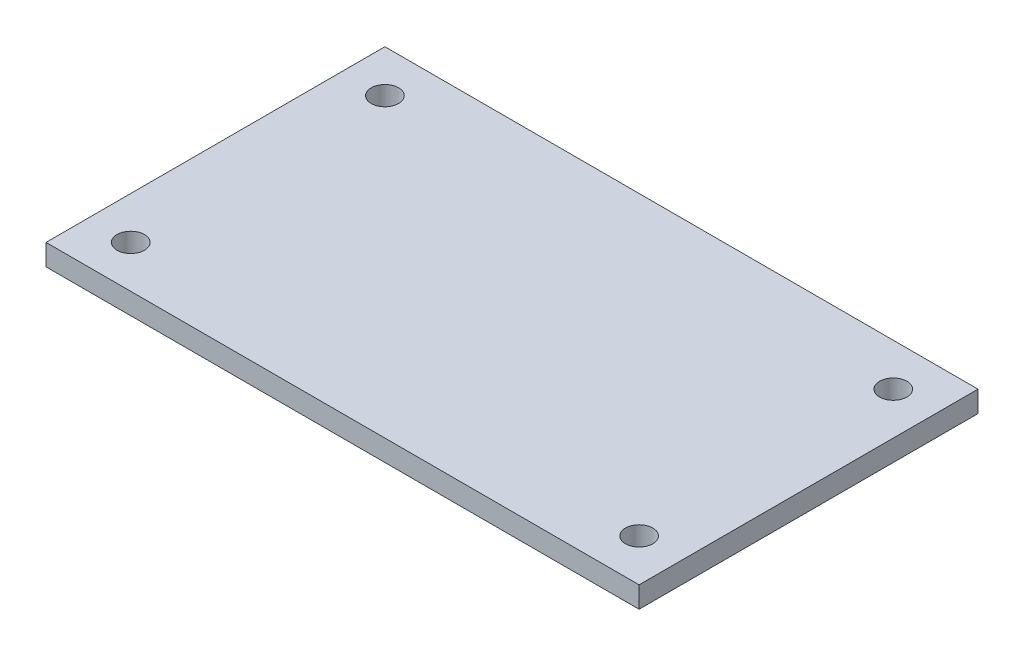
SolidWorks part; units mm, degrees
ref_plane "Front Plane" through (0, 0, 0) normal (0, 0, 1) x (1, 0, 0)
ref_plane "Top Plane" through (0, 0, 0) normal (0, 1, 0) x (1, 0, 0)
ref_plane "Right Plane" through (0, 0, 0) normal (1, 0, 0) x (0, 0, -1)
sketch "Sketch1" plane through (0, 0, 0) normal (0, 1, 0) x (1, 0, 0)
  line L0 (0, 50.8) -> (0, -50.8) construction
  line L1 (-88.9, -50.8) -> (88.9, -50.8)
  line L2 (-88.9, -50.8) -> (-88.9, 50.8)
  line L3 (-88.9, 50.8) -> (88.9, 50.8)
  line L4 (88.9, -50.8) -> (88.9, 50.8)
  line L5 (-88.9, -50.8) -> (88.9, 50.8) construction
  line L6 (-88.9, 50.8) -> (88.9, -50.8) construction
  line L7 (-88.9, 0) -> (88.9, 0) construction
  line L8 (-76.2, -50.8) -> (-76.2, 50.8) construction
  line L9 (76.2, -50.8) -> (76.2, 50.8) construction
  line L10 (-88.9, 38.1) -> (88.9, 38.1) construction
  line L11 (-88.9, -38.1) -> (88.9, -38.1) construction
  line L12 (-38.1, 50.8) -> (-38.1, -50.8) construction
  line L13 (38.1, 50.8) -> (38.1, -50.8) construction
  line L14 (-88.9, 25.4) -> (88.9, 25.4) construction
  line L15 (-88.9, -25.4) -> (88.9, -25.4) construction
  point P0 (0, 0)
  dimension "D1" = 177.8
  dimension "D2" = 101.6
  dimension "D3" = 12.7
  dimension "D4" = 12.7
  dimension "D5" = 12.7
  dimension "D6" = 12.7
  dimension "D7" = 38.1
  dimension "D8" = 38.1
  dimension "D9" = 25.4
  dimension "D10" = 25.4
extrude "Boss-Extrude1" add sketch "Sketch1" against normal blind 6.35
sketch "Sketch8" plane through (0, 0, 0) normal (0, 1, 0) x (1, 0, 0)
  line L0 (-76.2, -50.8) -> (-76.2, 50.8) construction
  line L1 (-88.9, -38.1) -> (88.9, -38.1) construction
  line L2 (76.2, -50.8) -> (76.2, 50.8) construction
  line L3 (-88.9, 38.1) -> (88.9, 38.1) construction
  point P0 (-76.2, -38.1)
  point P1 (76.2, -38.1)
  point P6 (76.2, 38.1)
  point P9 (-76.2, 38.1)
hole_wizard "P (0.323) Diameter Hole1" positions "Sketch9" profile "Sketch10" hole size "P" standard "ANSI Inch" end condition through all
sketch "Sketch9" plane through (0, 0, 0) normal (0, 1, 0) x (1, 0, 0)
  point P0 (-76.2, 38.1)
  point P3 (-76.2, -38.1)
  point P6 (76.2, -38.1)
  point P9 (76.2, 38.1)
sketch "Sketch10" plane through (-76.2, 0, -38.1) normal (1, 0, 0) x (0, 0, 1)
  line L0 (0, 0) -> (0, 6.35)
  line L1 (0, 6.35) -> (4.1021, 6.35)
  line L2 (4.1021, 6.35) -> (4.1021, 0)
  line L5 (4.1021, 0) -> (0, 0)
  line L11 (0, -6.35) -> (0, 107.95) construction
  dimension "Thru Hole Dia." = 8.2042
  dimension "Thru Hole Depth" = 6.35
